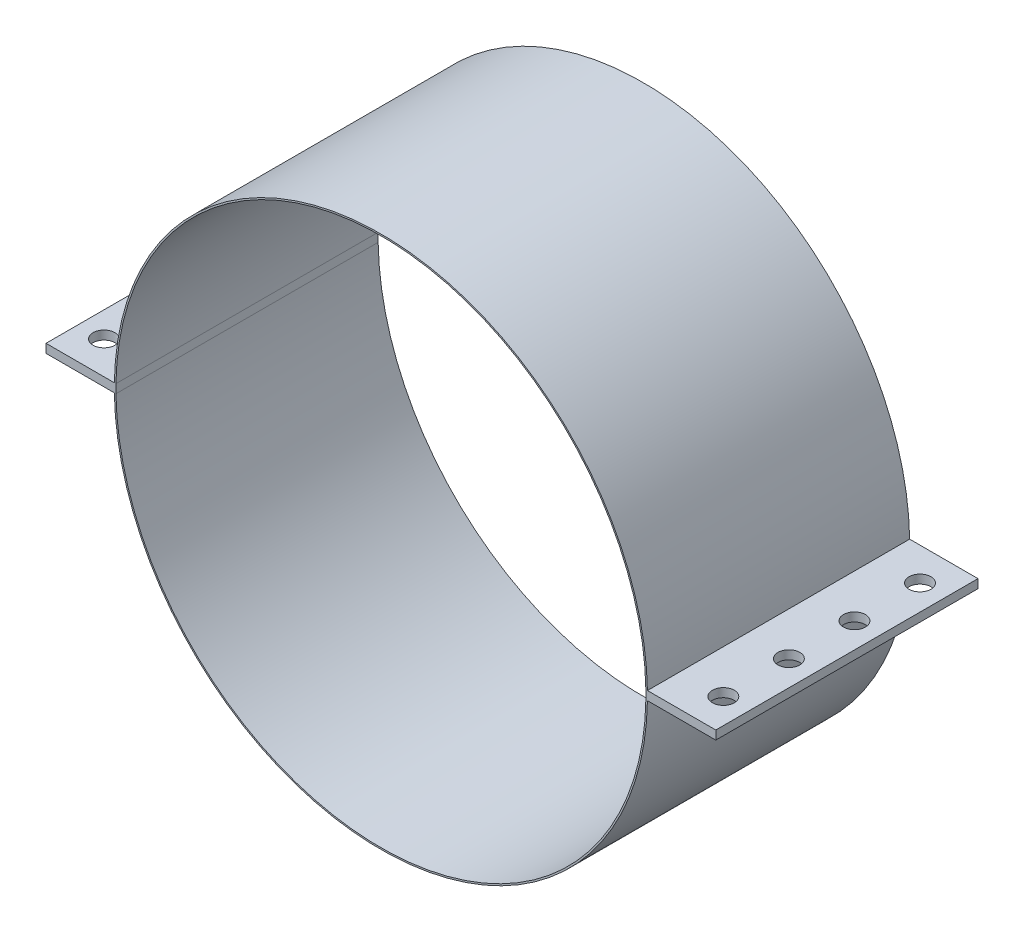
SolidWorks part; units mm, degrees
ref_plane "Front Plane" through (0, 0, 0) normal (0, 0, 1) x (1, 0, 0)
ref_plane "Top Plane" through (0, 0, 0) normal (0, 1, 0) x (1, 0, 0)
ref_plane "Right Plane" through (0, 0, 0) normal (1, 0, 0) x (0, 0, -1)
sketch "Sketch1" plane through (0, 0, 0) normal (0, 0, 1) x (1, 0, 0)
  circle A0 centre (0, 0) radius 77.47
  circle A1 centre (0, 0) radius 77.0128
  dimension "D1" = 154.94
  dimension "D2" = 154.0256
extrude "Boss-Extrude1" add sketch "Sketch1" along normal blind 76.2
sketch "Sketch2" plane through (0, 0, 76.2) normal (0, 0, 1) x (1, 0, 0)
  line L0 (0, 77.47) -> (0, -77.47) construction
  line L1 (77.0023, -1.27) -> (97.3223, -1.27)
  line L2 (77.0023, -1.27) -> (77.0023, 1.27)
  line L3 (77.0023, 1.27) -> (97.3223, 1.27)
  line L4 (97.3223, -1.27) -> (97.3223, 1.27)
  line L5 (-77.0023, 1.27) -> (-97.3223, 1.27)
  line L6 (-97.3223, -1.27) -> (-97.3223, 1.27)
  line L7 (-77.0023, -1.27) -> (-97.3223, -1.27)
  line L8 (-77.0023, -1.27) -> (-77.0023, 1.27)
  circle A0 centre (0, 0) radius 77.0128 construction
  circle A1 centre (0, 0) radius 77.47 construction
  point P6 (97.3223, 0)
  dimension "D1" = 2.54
  dimension "D2" = 20.32
extrude "Boss-Extrude2" add sketch "Sketch2" against normal blind 76.2
sketch "Sketch3" plane through (0, 1.27, 0) normal (0, 1, 0) x (1, 0, 0)
  line L0 (0, 0) -> (0, -76.2) construction
  line L1 (-77.4596, -76.2) -> (77.4596, -76.2) construction
  line L2 (87.391, 0) -> (87.391, -76.2)
  line L3 (97.3223, 0) -> (77.4596, 0) construction
  line L4 (97.3223, -76.2) -> (77.4596, -76.2) construction
  line L6 (77.4596, -76.2) -> (77.4596, 0) construction
  circle A0 centre (89.9953, -9.525) radius 3.175
  circle A1 centre (89.9953, -28.575) radius 3.175
  circle A2 centre (89.9953, -47.625) radius 3.175
  circle A3 centre (89.9953, -66.675) radius 3.175
  circle A4 centre (-89.9953, -9.525) radius 3.175
  circle A5 centre (-89.9953, -28.575) radius 3.175
  circle A6 centre (-89.9953, -47.625) radius 3.175
  circle A7 centre (-89.9953, -66.675) radius 3.175
  dimension "D1" = 6.35
  dimension "D2" = 9.525
  dimension "D5" = 12.5357
  dimension "D4" = 9.525
  dimension "D3" = 4
extrude "Cut-Extrude3" cut sketch "Sketch3" against normal blind 2.54 contours A7 | A6 | A5 | A4 | A0 | A1 | A2 | A3
